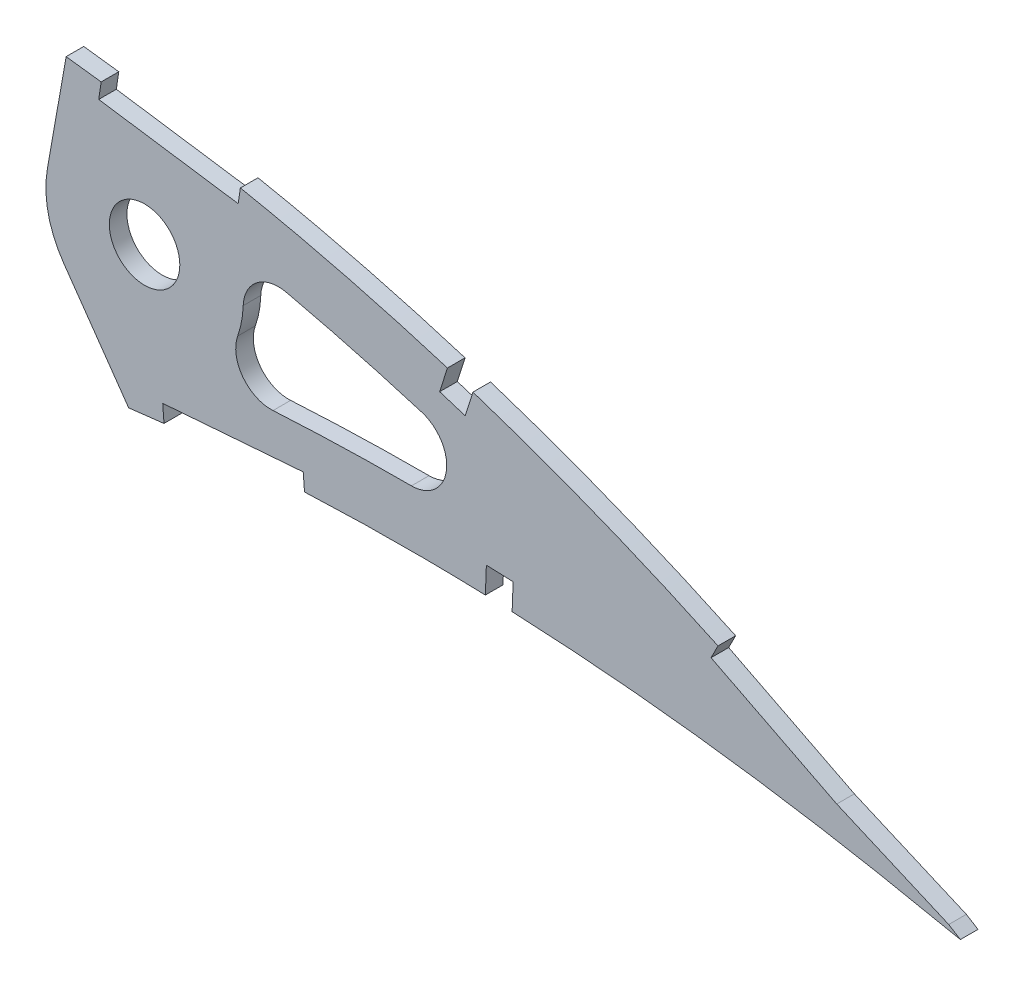
SolidWorks part; units mm, degrees
material "Plywood"
ref_plane "Front Plane" through (0, 0, 0) normal (0, 0, 1) x (1, 0, 0)
ref_plane "Top Plane" through (0, 0, 0) normal (0, 1, 0) x (1, 0, 0)
ref_plane "Right Plane" through (0, 0, 0) normal (1, 0, 0) x (0, 0, -1)
curve "Curve2"
  spline degree 3 poles (520.229, 0.8111, 0) (520.1892, 0.8357, 0) (520.0299, 0.9341, 0) (519.6711, 1.1542, 0) (519.0735, 1.5208, 0) (518.237, 2.0313, 0) (517.1622, 2.6844, 0) (515.8486, 3.4756, 0) (514.2969, 4.4021, 0) (512.5075, 5.4598, 0) (510.4807, 6.6436, 0) (508.2172, 7.9486, 0) (505.7172, 9.3676, 0) (502.9816, 10.8948, 0) (500.0114, 12.5227, 0) (496.8072, 14.2443, 0) (493.3701, 16.0505, 0) (489.7015, 17.9338, 0) (485.8019, 19.8836, 0) (481.6733, 21.8919, 0) (477.317, 23.9487, 0) (472.7345, 26.0429, 0) (467.9284, 28.1661, 0) (462.9001, 30.305, 0) (457.6524, 32.4505, 0) (452.1876, 34.5902, 0) (446.5089, 36.7144, 0) (440.6184, 38.8094, 0) (434.5207, 40.866, 0) (428.2186, 42.8708, 0) (421.7166, 44.813, 0) (415.0186, 46.68, 0) (408.1302, 48.4622, 0) (401.0555, 50.1466, 0) (393.8008, 51.7219, 0) (386.3718, 53.1787, 0) (378.7746, 54.5024, 0) (371.0303, 55.692, 0) (363.2636, 56.6815, 0) (355.5128, 57.652, 0) (347.7736, 58.5637, 0) (339.9398, 59.4368, 0) (332.019, 60.2663, 0) (324.019, 61.0497, 0) (315.9478, 61.7836, 0) (307.814, 62.4658, 0) (299.6253, 63.0925, 0) (291.3904, 63.6628, 0) (283.1174, 64.1714, 0) (274.8152, 64.6183, 0) (266.4922, 65.0001, 0) (258.157, 65.3142, 0) (249.8185, 65.5589, 0) (241.4854, 65.7316, 0) (233.1666, 65.8314, 0) (224.8708, 65.8555, 0) (216.6071, 65.8035, 0) (208.384, 65.6736, 0) (200.2107, 65.464, 0) (192.0958, 65.1743, 0) (184.048, 64.8046, 0) (176.0762, 64.3519, 0) (168.189, 63.8191, 0) (160.3952, 63.2038, 0) (152.7034, 62.506, 0) (145.1216, 61.7286, 0) (137.6583, 60.8693, 0) (130.3214, 59.9308, 0) (123.1191, 58.9147, 0) (116.0593, 57.8206, 0) (109.1496, 56.6517, 0) (102.3976, 55.409, 0) (95.8102, 54.0963, 0) (89.3948, 52.714, 0) (83.1581, 51.266, 0) (77.1065, 49.7551, 0) (71.2467, 48.1838, 0) (65.5845, 46.5561, 0) (60.1256, 44.8756, 0) (54.8764, 43.1442, 0) (49.8409, 41.3683, 0) (45.0253, 39.5493, 0) (40.4333, 37.6928, 0) (36.0702, 35.8014, 0) (31.9393, 33.8806, 0) (28.0452, 31.9329, 0) (24.3908, 29.9636, 0) (20.9797, 27.9757, 0) (17.8153, 25.973, 0) (14.8987, 23.9604, 0) (12.2341, 21.9394, 0) (9.8224, 19.9149, 0) (7.6651, 17.8901, 0) (5.7652, 15.8664, 0) (4.1228, 13.8473, 0) (2.7399, 11.8344, 0) (1.6168, 9.8297, 0) (0.7561, 7.8345, 0) (0.1568, 5.85, 0) (-0.1712, 3.8792, 0) (-0.2528, 1.9205, 0) (-0.0842, 0.6392, 0) (0, 0, 0) knots 0 0 0 0 0.000254 0.001015 0.002283 0.004057 0.006331 0.009105 0.012374 0.016134 0.02038 0.025106 0.030306 0.035972 0.0421 0.048678 0.055702 0.06316 0.071046 0.07935 0.088063 0.097176 0.106678 0.116562 0.126814 0.137428 0.148394 0.1597 0.171338 0.183298 0.19557 0.208144 0.221012 0.234162 0.247587 0.261277 0.275223 0.289414 0.303771 0.317689 0.331784 0.34604 0.360444 0.374983 0.38964 0.404403 0.419257 0.434187 0.449177 0.464215 0.479284 0.49437 0.509458 0.524532 0.539579 0.554583 0.56953 0.584403 0.599191 0.613877 0.628447 0.642889 0.657186 0.671326 0.685294 0.699078 0.712665 0.726043 0.739198 0.752118 0.764792 0.777208 0.789356 0.801224 0.812804 0.824083 0.835055 0.84571 0.856038 0.866034 0.875689 0.884998 0.893953 0.902553 0.910789 0.918661 0.926166 0.933303 0.940071 0.946475 0.952518 0.958205 0.963547 0.968557 0.97325 0.977651 0.981787 0.985694 0.989415 0.993001 0.996508 1 1 1 1
curve "Curve3"
  spline degree 3 poles (0, 0, 0) (0.1336, -0.6306, 0) (0.4014, -1.8948, 0) (1.129, -3.7148, 0) (2.0912, -5.4642, 0) (3.3081, -7.1386, 0) (4.7718, -8.7374, 0) (6.479, -10.2623, 0) (8.428, -11.7125, 0) (10.6162, -13.0874, 0) (13.0406, -14.3883, 0) (15.6982, -15.6145, 0) (18.5868, -16.7656, 0) (21.7032, -17.8401, 0) (25.0435, -18.8396, 0) (28.6046, -19.7616, 0) (32.3825, -20.6074, 0) (36.3735, -21.375, 0) (40.5732, -22.065, 0) (44.9774, -22.6771, 0) (49.5814, -23.2117, 0) (54.3808, -23.6676, 0) (59.3708, -24.0458, 0) (64.5464, -24.3466, 0) (69.9027, -24.5709, 0) (75.4344, -24.718, 0) (81.1363, -24.7899, 0) (87.003, -24.788, 0) (93.0289, -24.7115, 0) (99.2088, -24.5648, 0) (105.5368, -24.3469, 0) (112.0073, -24.0604, 0) (118.6142, -23.7083, 0) (125.3518, -23.2917, 0) (132.2141, -22.8125, 0) (139.1951, -22.2745, 0) (146.2885, -21.679, 0) (153.4882, -21.0296, 0) (160.7876, -20.3295, 0) (168.1806, -19.5808, 0) (175.6606, -18.7872, 0) (183.2209, -17.9512, 0) (190.8551, -17.0772, 0) (198.5563, -16.1668, 0) (206.3179, -15.2253, 0) (214.1326, -14.2544, 0) (221.9939, -13.2579, 0) (229.8947, -12.2404, 0) (237.8276, -11.2019, 0) (245.786, -10.1497, 0) (253.7621, -9.0829, 0) (261.7491, -8.0072, 0) (269.7395, -6.9257, 0) (277.7256, -5.8389, 0) (285.7003, -4.7513, 0) (293.6562, -3.6657, 0) (301.5856, -2.5824, 0) (309.4812, -1.5067, 0) (317.3352, -0.4385, 0) (325.1402, 0.6201, 0) (332.8888, 1.6659, 0) (340.5737, 2.6975, 0) (348.187, 3.7144, 0) (355.721, 4.7168, 0) (363.0553, 5.6745, 0) (370.1707, 6.6383, 0) (377.0913, 7.4284, 0) (383.9258, 8.1028, 0) (390.6811, 8.6557, 0) (397.3493, 9.0951, 0) (403.9227, 9.4241, 0) (410.3934, 9.6473, 0) (416.7532, 9.7713, 0) (422.9943, 9.7993, 0) (429.1081, 9.7402, 0) (435.0867, 9.5987, 0) (440.9216, 9.3813, 0) (446.6049, 9.0952, 0) (452.1283, 8.7483, 0) (457.4837, 8.3456, 0) (462.6634, 7.8966, 0) (467.6597, 7.4078, 0) (472.4647, 6.8849, 0) (477.0715, 6.3387, 0) (481.4727, 5.7729, 0) (485.6616, 5.1968, 0) (489.6316, 4.6162, 0) (493.3764, 4.0385, 0) (496.89, 3.4693, 0) (500.1667, 2.916, 0) (503.2016, 2.384, 0) (505.9892, 1.8782, 0) (508.5257, 1.4052, 0) (510.8062, 0.9673, 0) (512.8275, 0.5717, 0) (514.5859, 0.2202, 0) (516.0789, -0.0824, 0) (517.3037, -0.3347, 0) (518.2586, -0.5328, 0) (518.9417, -0.6767, 0) (519.3522, -0.7624, 0) (519.5346, -0.8013, 0) (519.5802, -0.8111, 0) knots 0 0 0 0 0.003638 0.007293 0.011028 0.014901 0.018963 0.023258 0.027821 0.032679 0.037853 0.043362 0.049215 0.055422 0.061989 0.068918 0.076211 0.083868 0.091887 0.100266 0.109 0.118085 0.127515 0.137285 0.147388 0.157816 0.168563 0.179619 0.190977 0.202627 0.21456 0.226767 0.239236 0.251959 0.264924 0.27812 0.291536 0.30516 0.318981 0.332985 0.347163 0.361499 0.375981 0.390597 0.405333 0.420175 0.43511 0.450124 0.465203 0.480333 0.495501 0.51069 0.525887 0.541078 0.556247 0.571382 0.586466 0.601485 0.616424 0.631269 0.646007 0.660621 0.675098 0.689423 0.703582 0.716908 0.730009 0.742952 0.755726 0.76832 0.780724 0.792927 0.804916 0.816679 0.828204 0.839475 0.850481 0.861208 0.871639 0.881763 0.891564 0.901027 0.910139 0.918884 0.927249 0.935221 0.942785 0.949928 0.956638 0.962904 0.968712 0.974054 0.978918 0.983297 0.98718 0.990561 0.993433 0.995791 0.99763 0.998946 0.999737 1 1 1 1
sketch "Sketch1" plane through (0, 0, 0) normal (0, 0, 1) x (1, 0, 0)
  line L1 (502.7977, -0.7849) -> (507.4667, -1.7115)
  line L2 (503.4256, 0.7849) -> (507.4667, -1.7115)
  spline S2 degree 3 poles (0, 0) (0.1293, -0.6103) (0.3884, -1.8336) (1.0925, -3.5948) (2.0236, -5.2877) (3.2013, -6.908) (4.6177, -8.4552) (6.2698, -9.9309) (8.1558, -11.3342) (10.2733, -12.6647) (12.6193, -13.9236) (15.1912, -15.1102) (17.9865, -16.2241) (21.0022, -17.2639) (24.2346, -18.231) (27.6807, -19.1233) (31.3366, -19.9418) (35.1986, -20.6846) (39.2627, -21.3523) (43.5246, -21.9446) (47.9799, -22.4619) (52.6243, -22.9031) (57.4531, -23.2691) (62.4616, -23.5602) (67.6448, -23.7773) (72.9979, -23.9196) (78.5156, -23.9892) (84.1928, -23.9873) (90.0241, -23.9133) (96.0044, -23.7713) (102.128, -23.5605) (108.3894, -23.2833) (114.783, -22.9425) (121.303, -22.5394) (127.9436, -22.0756) (134.6991, -21.555) (141.5634, -20.9788) (148.5305, -20.3504) (155.5942, -19.6728) (162.7484, -18.9484) (169.9867, -18.1804) (177.3029, -17.3713) (184.6905, -16.5256) (192.1429, -15.6446) (199.6538, -14.7335) (207.2161, -13.794) (214.8235, -12.8296) (222.4691, -11.845) (230.1458, -10.84) (237.8471, -9.8218) (245.5656, -8.7896) (253.2946, -7.7486) (261.0269, -6.702) (268.755, -5.6503) (276.4722, -4.5978) (284.1711, -3.5473) (291.8444, -2.499) (299.485, -1.458) (307.0852, -0.4243) (314.6382, 0.6001) (322.1365, 1.6121) (329.5732, 2.6104) (336.9406, 3.5944) (344.2312, 4.5645) (351.3286, 5.4912) (358.2142, 6.4239) (364.9113, 7.1885) (371.525, 7.8411) (378.0621, 8.3761) (384.5149, 8.8013) (390.876, 9.1197) (397.1377, 9.3357) (403.2921, 9.4557) (409.3316, 9.4828) (415.2479, 9.4256) (421.0334, 9.2887) (426.6799, 9.0783) (432.1795, 8.8014) (437.5246, 8.4657) (442.7069, 8.076) (447.7194, 7.6415) (452.5543, 7.1686) (457.2041, 6.6625) (461.6621, 6.134) (465.9211, 5.5865) (469.9748, 5.029) (473.8165, 4.4671) (477.4403, 3.9081) (480.8404, 3.3572) (484.0114, 2.8219) (486.9482, 2.3069) (489.6458, 1.8176) (492.1004, 1.3598) (494.3072, 0.9361) (496.2632, 0.5532) (497.9648, 0.2131) (499.4095, -0.0797) (500.5948, -0.3239) (501.5189, -0.5155) (502.1799, -0.6549) (502.5771, -0.7378) (502.7536, -0.7754) (502.7977, -0.7849) knots 0 0 0 0 0.003638 0.007293 0.011028 0.014901 0.018963 0.023258 0.027821 0.032679 0.037853 0.043362 0.049215 0.055422 0.061989 0.068918 0.076211 0.083868 0.091887 0.100266 0.109 0.118085 0.127515 0.137285 0.147388 0.157816 0.168563 0.179619 0.190977 0.202627 0.21456 0.226767 0.239236 0.251959 0.264924 0.27812 0.291536 0.30516 0.318981 0.332985 0.347163 0.361499 0.375981 0.390597 0.405333 0.420175 0.43511 0.450124 0.465203 0.480333 0.495501 0.51069 0.525887 0.541078 0.556247 0.571382 0.586466 0.601485 0.616424 0.631269 0.646007 0.660621 0.675098 0.689423 0.703582 0.716908 0.730009 0.742952 0.755726 0.76832 0.780724 0.792927 0.804916 0.816679 0.828204 0.839475 0.850481 0.861208 0.871639 0.881763 0.891564 0.901027 0.910139 0.918884 0.927249 0.935221 0.942785 0.949928 0.956638 0.962904 0.968712 0.974054 0.978918 0.983297 0.98718 0.990561 0.993433 0.995791 0.99763 0.998946 0.999737 1 1 1 1
  spline S3 degree 3 poles (503.4256, 0.7849) (503.3871, 0.8087) (503.2329, 0.9039) (502.8857, 1.1169) (502.3075, 1.4716) (501.498, 1.9657) (500.4579, 2.5977) (499.1867, 3.3633) (497.6851, 4.26) (495.9535, 5.2834) (493.9922, 6.429) (491.8018, 7.6919) (489.3825, 9.0651) (486.7353, 10.5429) (483.8611, 12.1183) (480.7604, 13.7842) (477.4343, 15.5321) (473.8841, 17.3545) (470.1105, 19.2413) (466.1153, 21.1848) (461.8997, 23.1751) (457.4652, 25.2017) (452.8143, 27.2563) (447.9484, 29.3262) (442.8702, 31.4023) (437.5819, 33.4729) (432.0866, 35.5285) (426.3865, 37.5558) (420.4857, 39.546) (414.3871, 41.4861) (408.0952, 43.3656) (401.6135, 45.1723) (394.9475, 46.8969) (388.1015, 48.5268) (381.0811, 50.0513) (373.8919, 51.461) (366.5401, 52.742) (359.046, 53.8931) (351.5302, 54.8507) (344.0298, 55.7898) (336.5405, 56.6721) (328.9598, 57.517) (321.2948, 58.3197) (313.5531, 59.0778) (305.7427, 59.788) (297.8716, 60.4482) (289.9474, 61.0547) (281.9785, 61.6064) (273.9728, 62.0987) (265.9387, 62.5311) (257.8845, 62.9006) (249.8186, 63.2046) (241.7494, 63.4413) (233.6854, 63.6085) (225.6353, 63.7051) (217.6075, 63.7284) (209.6107, 63.678) (201.6532, 63.5523) (193.7439, 63.3495) (185.8911, 63.0691) (178.1033, 62.7114) (170.3889, 62.2734) (162.7565, 61.7577) (155.2145, 61.1624) (147.7711, 60.4871) (140.4342, 59.7347) (133.2119, 58.9033) (126.1121, 57.995) (119.1423, 57.0118) (112.3106, 55.953) (105.6241, 54.8218) (99.0901, 53.6193) (92.7156, 52.349) (86.5074, 51.0113) (80.4721, 49.6101) (74.616, 48.148) (68.9454, 46.6275) (63.4661, 45.0524) (58.1835, 43.4261) (53.1039, 41.7506) (48.2311, 40.0321) (43.571, 38.2719) (39.1273, 36.4754) (34.9051, 34.645) (30.9076, 32.7863) (27.1393, 30.9015) (23.603, 28.9958) (20.3021, 27.0721) (17.2398, 25.134) (14.4175, 23.1865) (11.839, 21.2308) (9.5051, 19.2717) (7.4175, 17.3123) (5.579, 15.3539) (3.9896, 13.4) (2.6514, 11.4522) (1.5646, 9.5122) (0.7317, 7.5814) (0.1518, 5.6611) (-0.1657, 3.7539) (-0.2447, 1.8584) (-0.0814, 0.6186) (0, 0) knots 0 0 0 0 0.000254 0.001015 0.002283 0.004057 0.006331 0.009105 0.012374 0.016134 0.02038 0.025106 0.030306 0.035972 0.0421 0.048678 0.055702 0.06316 0.071046 0.07935 0.088063 0.097176 0.106678 0.116562 0.126814 0.137428 0.148394 0.1597 0.171338 0.183298 0.19557 0.208144 0.221012 0.234162 0.247587 0.261277 0.275223 0.289414 0.303771 0.317689 0.331784 0.34604 0.360444 0.374983 0.38964 0.404403 0.419257 0.434187 0.449177 0.464215 0.479284 0.49437 0.509458 0.524532 0.539579 0.554583 0.56953 0.584403 0.599191 0.613877 0.628447 0.642889 0.657186 0.671326 0.685294 0.699078 0.712665 0.726043 0.739198 0.752118 0.764792 0.777208 0.789356 0.801224 0.812804 0.824083 0.835055 0.84571 0.856038 0.866034 0.875689 0.884998 0.893953 0.902553 0.910789 0.918661 0.926166 0.933303 0.940071 0.946475 0.952518 0.958205 0.963547 0.968557 0.97325 0.977651 0.981787 0.985694 0.989415 0.993001 0.996508 1 1 1 1
extrude "Boss-Extrude1" add sketch "Sketch1" along normal blind 3.175
sketch "Sketch4" plane through (0, 0, 3.175) normal (0, 0, 1) x (1, 0, 0)
  line L0 (342.9777, 36.32) -> (346.3588, 55.4952)
  line L1 (345.923, 23.0344) -> (357.6226, 6.3256)
  line L2 (360.4876, 33.2326) -> (390.7312, 33.2326)
  circle A0 centre (360.4876, 33.2326) radius 17.78
  circle A1 centre (360.4876, 33.2326) radius 6.35
  spline S0 degree 3 poles (-1939.359, -486.1193) (49.033, 56.5957) (-7.3857, 17.6121) (1.0925, -3.5948) (2.0236, -5.2877) (3.2013, -6.908) (4.6177, -8.4552) (6.2698, -9.9309) (8.1558, -11.3342) (10.2733, -12.6647) (12.6193, -13.9236) (15.1912, -15.1102) (17.9865, -16.2241) (21.0022, -17.2639) (24.2346, -18.231) (27.6807, -19.1233) (31.3366, -19.9418) (35.1986, -20.6846) (39.2627, -21.3523) (43.5246, -21.9446) (47.9799, -22.4619) (52.6243, -22.9031) (57.4531, -23.2691) (62.4616, -23.5602) (67.6448, -23.7773) (72.9979, -23.9196) (78.5156, -23.9892) (84.1928, -23.9873) (90.0241, -23.9133) (96.0044, -23.7713) (102.128, -23.5605) (108.3894, -23.2833) (114.783, -22.9425) (121.303, -22.5394) (127.9436, -22.0756) (134.6991, -21.555) (141.5634, -20.9788) (148.5305, -20.3504) (155.5942, -19.6728) (162.7484, -18.9484) (169.9867, -18.1804) (177.3029, -17.3713) (184.6905, -16.5256) (192.1429, -15.6446) (199.6538, -14.7335) (207.2161, -13.794) (214.8235, -12.8296) (222.4691, -11.845) (230.1458, -10.84) (237.8471, -9.8218) (245.5656, -8.7896) (253.2946, -7.7486) (261.0269, -6.702) (268.755, -5.6503) (276.4722, -4.5978) (284.1711, -3.5473) (291.8444, -2.499) (299.485, -1.458) (307.0852, -0.4243) (314.6382, 0.6001) (322.1365, 1.6121) (329.5732, 2.6104) (336.9406, 3.5944) (344.2312, 4.5645) (351.3286, 5.4912) (358.2142, 6.4239) (364.9113, 7.1885) (371.525, 7.8411) (378.0621, 8.3761) (384.5149, 8.8013) (390.876, 9.1197) (397.1377, 9.3357) (403.2921, 9.4557) (409.3316, 9.4828) (415.2479, 9.4256) (421.0334, 9.2887) (426.6799, 9.0783) (432.1795, 8.8014) (437.5246, 8.4657) (442.7069, 8.076) (447.7194, 7.6415) (452.5543, 7.1686) (457.2041, 6.6625) (461.6621, 6.134) (465.9211, 5.5865) (469.9748, 5.029) (473.8165, 4.4671) (477.4403, 3.9081) (480.8404, 3.3572) (484.0114, 2.8219) (486.9482, 2.3069) (489.6458, 1.8176) (492.1004, 1.3598) (494.3072, 0.9361) (496.2632, 0.5532) (497.9648, 0.2131) (499.4095, -0.0797) (500.5948, -0.3239) (501.5189, -0.5155) (502.1799, -0.6549) (517.7197, -3.8983) (531.8047, -12.9312) (961.8177, 1945.365) knots -0.121768 -0.121768 -0.121768 -0.121768 0.003638 0.007293 0.011028 0.014901 0.018963 0.023258 0.027821 0.032679 0.037853 0.043362 0.049215 0.055422 0.061989 0.068918 0.076211 0.083868 0.091887 0.100266 0.109 0.118085 0.127515 0.137285 0.147388 0.157816 0.168563 0.179619 0.190977 0.202627 0.21456 0.226767 0.239236 0.251959 0.264924 0.27812 0.291536 0.30516 0.318981 0.332985 0.347163 0.361499 0.375981 0.390597 0.405333 0.420175 0.43511 0.450124 0.465203 0.480333 0.495501 0.51069 0.525887 0.541078 0.556247 0.571382 0.586466 0.601485 0.616424 0.631269 0.646007 0.660621 0.675098 0.689423 0.703582 0.716908 0.730009 0.742952 0.755726 0.76832 0.780724 0.792927 0.804916 0.816679 0.828204 0.839475 0.850481 0.861208 0.871639 0.881763 0.891564 0.901027 0.910139 0.918884 0.927249 0.935221 0.942785 0.949928 0.956638 0.962904 0.968712 0.974054 0.978918 0.983297 0.98718 0.990561 0.993433 0.995791 0.99763 0.998946 0.999737 1.090356 1.090356 1.090356 1.090356 only from (0, 0) to (502.7977, -0.7849) construction
  spline S1 degree 3 poles (1596.0847, 1675.4542) (530.0817, -21.8378) (517.9824, -8.1433) (502.8857, 1.1169) (502.3075, 1.4716) (501.498, 1.9657) (500.4579, 2.5977) (499.1867, 3.3633) (497.6851, 4.26) (495.9535, 5.2834) (493.9922, 6.429) (491.8018, 7.6919) (489.3825, 9.0651) (486.7353, 10.5429) (483.8611, 12.1183) (480.7604, 13.7842) (477.4343, 15.5321) (473.8841, 17.3545) (470.1105, 19.2413) (466.1153, 21.1848) (461.8997, 23.1751) (457.4652, 25.2017) (452.8143, 27.2563) (447.9484, 29.3262) (442.8702, 31.4023) (437.5819, 33.4729) (432.0866, 35.5285) (426.3865, 37.5558) (420.4857, 39.546) (414.3871, 41.4861) (408.0952, 43.3656) (401.6135, 45.1723) (394.9475, 46.8969) (388.1015, 48.5268) (381.0811, 50.0513) (373.8919, 51.461) (366.5401, 52.742) (359.046, 53.8931) (351.5302, 54.8507) (344.0298, 55.7898) (336.5405, 56.6721) (328.9598, 57.517) (321.2948, 58.3197) (313.5531, 59.0778) (305.7427, 59.788) (297.8716, 60.4482) (289.9474, 61.0547) (281.9785, 61.6064) (273.9728, 62.0987) (265.9387, 62.5311) (257.8845, 62.9006) (249.8186, 63.2046) (241.7494, 63.4413) (233.6854, 63.6085) (225.6353, 63.7051) (217.6075, 63.7284) (209.6107, 63.678) (201.6532, 63.5523) (193.7439, 63.3495) (185.8911, 63.0691) (178.1033, 62.7114) (170.3889, 62.2734) (162.7565, 61.7577) (155.2145, 61.1624) (147.7711, 60.4871) (140.4342, 59.7347) (133.2119, 58.9033) (126.1121, 57.995) (119.1423, 57.0118) (112.3106, 55.953) (105.6241, 54.8218) (99.0901, 53.6193) (92.7156, 52.349) (86.5074, 51.0113) (80.4721, 49.6101) (74.616, 48.148) (68.9454, 46.6275) (63.4661, 45.0524) (58.1835, 43.4261) (53.1039, 41.7506) (48.2311, 40.0321) (43.571, 38.2719) (39.1273, 36.4754) (34.9051, 34.645) (30.9076, 32.7863) (27.1393, 30.9015) (23.603, 28.9958) (20.3021, 27.0721) (17.2398, 25.134) (14.4175, 23.1865) (11.839, 21.2308) (9.5051, 19.2717) (7.4175, 17.3123) (5.579, 15.3539) (3.9896, 13.4) (2.6514, 11.4522) (1.5646, 9.5122) (0.7317, 7.5814) (0.1518, 5.6611) (-0.1657, 3.7539) (-1.1153, -19.0274) (65.1985, -36.9717) (-1990.693, -186.6939) knots -0.096988 -0.096988 -0.096988 -0.096988 0.000254 0.001015 0.002283 0.004057 0.006331 0.009105 0.012374 0.016134 0.02038 0.025106 0.030306 0.035972 0.0421 0.048678 0.055702 0.06316 0.071046 0.07935 0.088063 0.097176 0.106678 0.116562 0.126814 0.137428 0.148394 0.1597 0.171338 0.183298 0.19557 0.208144 0.221012 0.234162 0.247587 0.261277 0.275223 0.289414 0.303771 0.317689 0.331784 0.34604 0.360444 0.374983 0.38964 0.404403 0.419257 0.434187 0.449177 0.464215 0.479284 0.49437 0.509458 0.524532 0.539579 0.554583 0.56953 0.584403 0.599191 0.613877 0.628447 0.642889 0.657186 0.671326 0.685294 0.699078 0.712665 0.726043 0.739198 0.752118 0.764792 0.777208 0.789356 0.801224 0.812804 0.824083 0.835055 0.84571 0.856038 0.866034 0.875689 0.884998 0.893953 0.902553 0.910789 0.918661 0.926166 0.933303 0.940071 0.946475 0.952518 0.958205 0.963547 0.968557 0.97325 0.977651 0.981787 0.985694 0.989415 0.993001 0.996508 1.116632 1.116632 1.116632 1.116632 only from (503.4256, 0.7849) to (0, 0) construction
  spline S2 degree 3 poles (0, 0) (0.1293, -0.6103) (0.3884, -1.8336) (1.0925, -3.5948) (2.0236, -5.2877) (3.2013, -6.908) (4.6177, -8.4552) (6.2698, -9.9309) (8.1558, -11.3342) (10.2733, -12.6647) (12.6193, -13.9236) (15.1912, -15.1102) (17.9865, -16.2241) (21.0022, -17.2639) (24.2346, -18.231) (27.6807, -19.1233) (31.3366, -19.9418) (35.1986, -20.6846) (39.2627, -21.3523) (43.5246, -21.9446) (47.9799, -22.4619) (52.6243, -22.9031) (57.4531, -23.2691) (62.4616, -23.5602) (67.6448, -23.7773) (72.9979, -23.9196) (78.5156, -23.9892) (84.1928, -23.9873) (90.0241, -23.9133) (96.0044, -23.7713) (102.128, -23.5605) (108.3894, -23.2833) (114.783, -22.9425) (121.303, -22.5394) (127.9436, -22.0756) (134.6991, -21.555) (141.5634, -20.9788) (148.5305, -20.3504) (155.5942, -19.6728) (162.7484, -18.9484) (169.9867, -18.1804) (177.3029, -17.3713) (184.6905, -16.5256) (192.1429, -15.6446) (199.6538, -14.7335) (207.2161, -13.794) (214.8235, -12.8296) (222.4691, -11.845) (230.1458, -10.84) (237.8471, -9.8218) (245.5656, -8.7896) (253.2946, -7.7486) (261.0269, -6.702) (268.755, -5.6503) (276.4722, -4.5978) (284.1711, -3.5473) (291.8444, -2.499) (299.485, -1.458) (307.0852, -0.4243) (314.6382, 0.6001) (322.1365, 1.6121) (329.5732, 2.6104) (336.9406, 3.5944) (344.2312, 4.5645) (351.3286, 5.4912) (358.2142, 6.4239) (364.9113, 7.1885) (371.525, 7.8411) (378.0621, 8.3761) (384.5149, 8.8013) (390.876, 9.1197) (397.1377, 9.3357) (403.2921, 9.4557) (409.3316, 9.4828) (415.2479, 9.4256) (421.0334, 9.2887) (426.6799, 9.0783) (432.1795, 8.8014) (437.5246, 8.4657) (442.7069, 8.076) (447.7194, 7.6415) (452.5543, 7.1686) (457.2041, 6.6625) (461.6621, 6.134) (465.9211, 5.5865) (469.9748, 5.029) (473.8165, 4.4671) (477.4403, 3.9081) (480.8404, 3.3572) (484.0114, 2.8219) (486.9482, 2.3069) (489.6458, 1.8176) (492.1004, 1.3598) (494.3072, 0.9361) (496.2632, 0.5532) (497.9648, 0.2131) (499.4095, -0.0797) (500.5948, -0.3239) (501.5189, -0.5155) (502.1799, -0.6549) (502.5771, -0.7378) (502.7536, -0.7754) (502.7977, -0.7849) knots 0 0 0 0 0.003638 0.007293 0.011028 0.014901 0.018963 0.023258 0.027821 0.032679 0.037853 0.043362 0.049215 0.055422 0.061989 0.068918 0.076211 0.083868 0.091887 0.100266 0.109 0.118085 0.127515 0.137285 0.147388 0.157816 0.168563 0.179619 0.190977 0.202627 0.21456 0.226767 0.239236 0.251959 0.264924 0.27812 0.291536 0.30516 0.318981 0.332985 0.347163 0.361499 0.375981 0.390597 0.405333 0.420175 0.43511 0.450124 0.465203 0.480333 0.495501 0.51069 0.525887 0.541078 0.556247 0.571382 0.586466 0.601485 0.616424 0.631269 0.646007 0.660621 0.675098 0.689423 0.703582 0.716908 0.730009 0.742952 0.755726 0.76832 0.780724 0.792927 0.804916 0.816679 0.828204 0.839475 0.850481 0.861208 0.871639 0.881763 0.891564 0.901027 0.910139 0.918884 0.927249 0.935221 0.942785 0.949928 0.956638 0.962904 0.968712 0.974054 0.978918 0.983297 0.98718 0.990561 0.993433 0.995791 0.99763 0.998946 0.999737 1 1 1 1
  spline S3 degree 3 poles (503.4256, 0.7849) (503.3871, 0.8087) (503.2329, 0.9039) (502.8857, 1.1169) (502.3075, 1.4716) (501.498, 1.9657) (500.4579, 2.5977) (499.1867, 3.3633) (497.6851, 4.26) (495.9535, 5.2834) (493.9922, 6.429) (491.8018, 7.6919) (489.3825, 9.0651) (486.7353, 10.5429) (483.8611, 12.1183) (480.7604, 13.7842) (477.4343, 15.5321) (473.8841, 17.3545) (470.1105, 19.2413) (466.1153, 21.1848) (461.8997, 23.1751) (457.4652, 25.2017) (452.8143, 27.2563) (447.9484, 29.3262) (442.8702, 31.4023) (437.5819, 33.4729) (432.0866, 35.5285) (426.3865, 37.5558) (420.4857, 39.546) (414.3871, 41.4861) (408.0952, 43.3656) (401.6135, 45.1723) (394.9475, 46.8969) (388.1015, 48.5268) (381.0811, 50.0513) (373.8919, 51.461) (366.5401, 52.742) (359.046, 53.8931) (351.5302, 54.8507) (344.0298, 55.7898) (336.5405, 56.6721) (328.9598, 57.517) (321.2948, 58.3197) (313.5531, 59.0778) (305.7427, 59.788) (297.8716, 60.4482) (289.9474, 61.0547) (281.9785, 61.6064) (273.9728, 62.0987) (265.9387, 62.5311) (257.8845, 62.9006) (249.8186, 63.2046) (241.7494, 63.4413) (233.6854, 63.6085) (225.6353, 63.7051) (217.6075, 63.7284) (209.6107, 63.678) (201.6532, 63.5523) (193.7439, 63.3495) (185.8911, 63.0691) (178.1033, 62.7114) (170.3889, 62.2734) (162.7565, 61.7577) (155.2145, 61.1624) (147.7711, 60.4871) (140.4342, 59.7347) (133.2119, 58.9033) (126.1121, 57.995) (119.1423, 57.0118) (112.3106, 55.953) (105.6241, 54.8218) (99.0901, 53.6193) (92.7156, 52.349) (86.5074, 51.0113) (80.4721, 49.6101) (74.616, 48.148) (68.9454, 46.6275) (63.4661, 45.0524) (58.1835, 43.4261) (53.1039, 41.7506) (48.2311, 40.0321) (43.571, 38.2719) (39.1273, 36.4754) (34.9051, 34.645) (30.9076, 32.7863) (27.1393, 30.9015) (23.603, 28.9958) (20.3021, 27.0721) (17.2398, 25.134) (14.4175, 23.1865) (11.839, 21.2308) (9.5051, 19.2717) (7.4175, 17.3123) (5.579, 15.3539) (3.9896, 13.4) (2.6514, 11.4522) (1.5646, 9.5122) (0.7317, 7.5814) (0.1518, 5.6611) (-0.1657, 3.7539) (-0.2447, 1.8584) (-0.0814, 0.6186) (0, 0) knots 0 0 0 0 0.000254 0.001015 0.002283 0.004057 0.006331 0.009105 0.012374 0.016134 0.02038 0.025106 0.030306 0.035972 0.0421 0.048678 0.055702 0.06316 0.071046 0.07935 0.088063 0.097176 0.106678 0.116562 0.126814 0.137428 0.148394 0.1597 0.171338 0.183298 0.19557 0.208144 0.221012 0.234162 0.247587 0.261277 0.275223 0.289414 0.303771 0.317689 0.331784 0.34604 0.360444 0.374983 0.38964 0.404403 0.419257 0.434187 0.449177 0.464215 0.479284 0.49437 0.509458 0.524532 0.539579 0.554583 0.56953 0.584403 0.599191 0.613877 0.628447 0.642889 0.657186 0.671326 0.685294 0.699078 0.712665 0.726043 0.739198 0.752118 0.764792 0.777208 0.789356 0.801224 0.812804 0.824083 0.835055 0.84571 0.856038 0.866034 0.875689 0.884998 0.893953 0.902553 0.910789 0.918661 0.926166 0.933303 0.940071 0.946475 0.952518 0.958205 0.963547 0.968557 0.97325 0.977651 0.981787 0.985694 0.989415 0.993001 0.996508 1 1 1 1
  spline S4 degree 1 poles (498.0859, -7.8588) (10.022, 1.7185) knots 0 0 1 1 construction
  spline S5 degree 1 poles (10.022, 1.7185) (504.9173, 9.1516) knots 0 0 1 1 construction
  spline S6 degree 3 poles (498.0859, -7.8588) (497.9469, -7.7729) (497.6755, -7.6063) (497.0745, -7.2376) (496.073, -6.6257) (494.034, -5.3896) (489.9509, -2.9592) (481.7087, 1.7828) (464.948, 10.7477) (440.2507, 22.0083) (414.6791, 31.031) (393.8046, 36.8155) (380.602, 39.8235) (369.9822, 41.8499) (361.9478, 43.1977) (353.9876, 44.3116) (345.6865, 45.3455) (337.4905, 46.3384) (326.5045, 47.5759) (307.2867, 49.5386) (279.7715, 51.732) (246.7179, 53.3195) (213.6646, 53.7552) (180.6691, 52.9014) (147.8152, 50.5632) (120.6625, 47.1646) (99.1877, 43.3787) (83.2589, 39.9382) (67.5746, 35.8064) (54.8041, 31.6869) (44.8785, 27.8959) (37.6273, 24.7728) (30.6423, 21.3346) (24.0439, 17.5382) (18.0447, 13.3493) (13.8923, 9.5446) (11.5209, 6.5233) (10.5748, 4.8197) (10.1543, 3.6588) (10.0297, 3.1195) (9.9672, 2.6225) (9.9572, 2.3998) (9.9588, 2.3191) (9.9601, 2.2824) (9.9755, 2.1081) (9.998, 1.9117) (10.0142, 1.7801) (10.022, 1.7185) knots 0 0 0 0 0.000976 0.001952 0.003903 0.007806 0.015612 0.031224 0.062448 0.124896 0.187344 0.218568 0.249792 0.265404 0.281016 0.296629 0.312241 0.327853 0.343465 0.374689 0.437137 0.499585 0.562033 0.624481 0.686929 0.749377 0.780601 0.811825 0.843049 0.874274 0.889886 0.905498 0.92111 0.936722 0.952334 0.967946 0.975752 0.983558 0.987461 0.991364 0.993315 0.995267 0.996242 0.997218 0.998194 0.998682 0.99917 0.99917 0.99917 0.99917
  spline S7 degree 3 poles (10.022, 1.7185) (10.0347, 1.6599) (10.0621, 1.5353) (10.1053, 1.3469) (10.1485, 1.1764) (10.1634, 1.1269) (10.1846, 1.0623) (10.2582, 0.8739) (10.471, 0.4378) (10.7582, -0.0307) (11.4745, -0.9405) (12.8348, -2.2117) (15.8465, -4.2506) (20.7309, -6.5276) (27.4244, -8.6509) (34.5678, -10.2856) (41.9694, -11.5214) (49.5311, -12.4386) (59.7521, -13.3077) (72.7026, -13.8464) (88.3798, -13.8504) (104.1321, -13.363) (125.1917, -12.1985) (151.5744, -9.9789) (183.2656, -6.5394) (214.9809, -2.61) (246.7126, 1.5971) (278.4754, 5.9283) (304.9613, 9.5471) (323.5218, 12.0515) (334.1258, 13.4688) (340.757, 14.3528) (346.0757, 15.0514) (350.0239, 15.5708) (353.9954, 16.1055) (358.0945, 16.6309) (362.1894, 17.1023) (367.6256, 17.6763) (377.1849, 18.5459) (390.8533, 19.3786) (412.7664, 19.8538) (440.1321, 18.8575) (467.3149, 15.8619) (486.1639, 12.8099) (495.5577, 11.0534) (499.8832, 10.1925) (501.9026, 9.7801) (502.8845, 9.5777) (503.7571, 9.3959) (504.3754, 9.2659) (504.7415, 9.1891) (504.9173, 9.1516) knots 0.000865 0.000865 0.000865 0.000865 0.001353 0.00184 0.002816 0.003792 0.004768 0.006719 0.008671 0.012573 0.016476 0.024282 0.032088 0.047699 0.063311 0.078922 0.094534 0.110145 0.125757 0.15698 0.188203 0.219426 0.250649 0.313095 0.37554 0.437986 0.500432 0.562878 0.625324 0.656547 0.672159 0.68777 0.695576 0.703382 0.711187 0.718993 0.726799 0.734605 0.750216 0.781439 0.812662 0.875108 0.937554 0.968777 0.984389 0.992194 0.994146 0.996097 0.998049 0.999024 1 1 1 1
  dimension "D1" = 35.56
  dimension "D3" = 80
  dimension "D4" = 55
  dimension "D2" = 10.16
extrude "Cut-Extrude2" cut sketch "Sketch4" against normal blind 7.62
sketch "Sketch5" plane through (0, 0, 3.175) normal (0, 0, 1) x (1, 0, 0)
  line L1 (352.6921, 54.8905) -> (352.2294, 51.7498)
  line L3 (377.8179, 51.1893) -> (352.6921, 54.8905)
  line L5 (415.1161, 41.459) -> (413.6569, 36.8603)
  line L7 (422.066, 14.0099) -> (421.8846, 9.1885)
  line L9 (426.8874, 13.8284) -> (422.066, 14.0099)
  line L11 (419.7148, 39.9998) -> (415.1161, 41.459)
  line L13 (463.9822, 22.6301) -> (462.5448, 19.7991)
  line L15 (486.5411, 11.1759) -> (463.9822, 22.6301)
  line L17 (509.7692, 1.1434) -> (486.5411, 11.1759)
  line L19 (389.0717, 12.0535) -> (363.7545, 10.0956)
  line L21 (363.7545, 10.0956) -> (363.9992, 6.9309)
  line L23 (363.9992, 6.9309) -> (389.3165, 8.8889)
  line L25 (389.3165, 8.8889) -> (389.0717, 12.0535)
  line L27 (352.2294, 51.7498) -> (377.3553, 48.0485)
  line L29 (377.3553, 48.0485) -> (377.8179, 51.1893)
  line L31 (421.8846, 9.1885) -> (426.706, 9.007)
  line L33 (426.706, 9.007) -> (426.8874, 13.8284)
  line L35 (413.6569, 36.8603) -> (418.2556, 35.4011)
  line L37 (418.2556, 35.4011) -> (419.7148, 39.9998)
  line L39 (462.5448, 19.7991) -> (485.1923, 8.3)
  line L41 (485.1923, 8.3) -> (508.5102, -1.7713)
  line L43 (508.5102, -1.7713) -> (509.7692, 1.1434)
extrude "Cut-Extrude3" cut sketch "Sketch5" against normal blind 7.62
fillet "Fillet1" radius 6.35 3 edges at (449.31, 17.6882, 1.5875) (369.3635, 17.8265, 1.5875) (376.692, 40.55, 1.5875)
move or copy body "Body-Move/Copy1" [suppressed] bodies to move or copy 118 parameters "D1"=0, "D2"=0, "D3"=0
